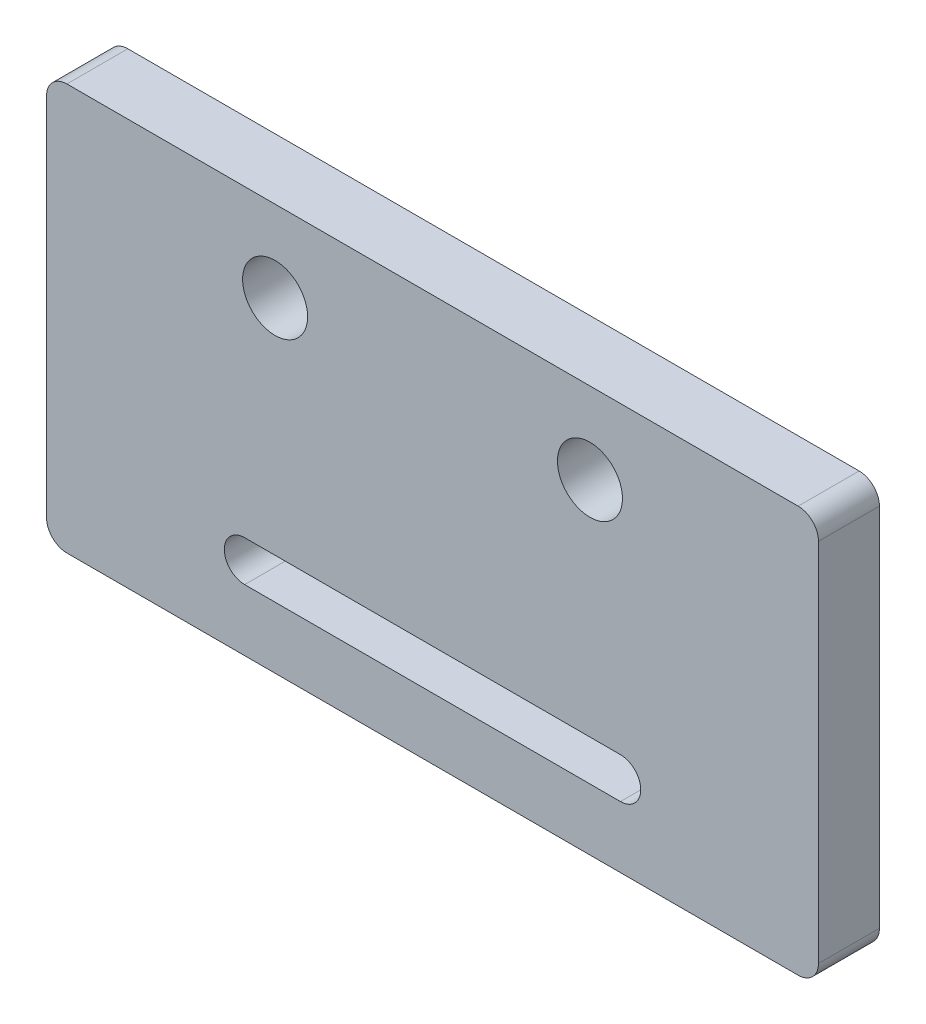
SolidWorks part; units mm, degrees
material "Pine"
ref_plane "Front Plane" through (0, 0, 0) normal (0, 0, 1) x (1, 0, 0)
ref_plane "Top Plane" through (0, 0, 0) normal (0, 1, 0) x (1, 0, 0)
ref_plane "Right Plane" through (0, 0, 0) normal (1, 0, 0) x (0, 0, -1)
sketch "Sketch1" plane through (0, 0, 0) normal (0, 0, 1) x (1, 0, 0)
  line L1 (0, 0) -> (-38, 0)
  line L2 (0, 0) -> (0, 20)
  line L3 (0, 20) -> (-38, 20)
  line L4 (-38, 0) -> (-38, 20)
  dimension "D1" = 38
  dimension "D2" = 20
extrude "Boss-Extrude1" add sketch "Sketch1" along normal blind 3
hole_wizard "M3 Clearance Hole1" positions "Sketch3" profile "Sketch2" hole size "M3" standard "ISO"
sketch "Sketch3" plane through (0, 0, 3) normal (0, 0, 1) x (1, 0, 0)
  line L0 (0, 0) -> (0, 20) construction
  line L2 (0, 20) -> (-38, 20) construction
  point P0 (-11.25, 16)
  point P2 (-26.75, 16)
  dimension "D1" = 15.5
  dimension "D2" = 11.25
  dimension "D3" = 4
  dimension "D4" = 4
sketch "Sketch2" plane through (-11.25, 16, 3) normal (1, 0, 0) x (0, -1, 0)
  line L0 (0, 0) -> (0, 20.9614)
  line L1 (0, 20.9614) -> (1.6, 20)
  line L2 (1.6, 20) -> (1.6, 0)
  line L5 (1.6, 0) -> (0, 0)
  line L10 (0, 20.9614) -> (-1.6, 20) construction
  line L11 (0, -6.35) -> (0, 107.95) construction
  dimension "Hole Dia." = 3.2
  dimension "Hole Depth" = 20
  dimension "Drill Angle" = 118
sketch "Sketch4" plane through (0, 0, 3) normal (0, 0, 1) x (1, 0, 0)
  line L0 (-11.25, 14.4) -> (-11.25, 5.4)
  line L1 (-11.25, 5.4) -> (-11.25, 4.03)
  line L2 (-11.25, 4.03) -> (-9.75, 4.03)
  line L3 (-11.25, 4.03) -> (-26.75, 4.03)
  line L4 (-26.75, 4.03) -> (-28.25, 4.03)
  line L6 (-9.75, 5.03) -> (-28.25, 5.03)
  line L7 (-9.75, 3.03) -> (-28.25, 3.03)
  circle A0 centre (-11.25, 16) radius 1.6 construction
  circle A1 centre (-28.25, 4.03) radius 1
  circle A2 centre (-9.75, 4.03) radius 1
  dimension "D5" = 2
  dimension "D6" = 2
  dimension "D1" = 9
  dimension "D2" = 1.5
  dimension "D3" = 1.5
  dimension "D4" = 15.5
  dimension "D7" = 1.37
extrude "Cut-Extrude1" cut sketch "Sketch4" against normal blind 3
fillet "Fillet1" radius 1 4 edges at (-38, 0, 1.5) (0, 0, 1.5) (0, 20, 1.5) (-38, 20, 1.5)
